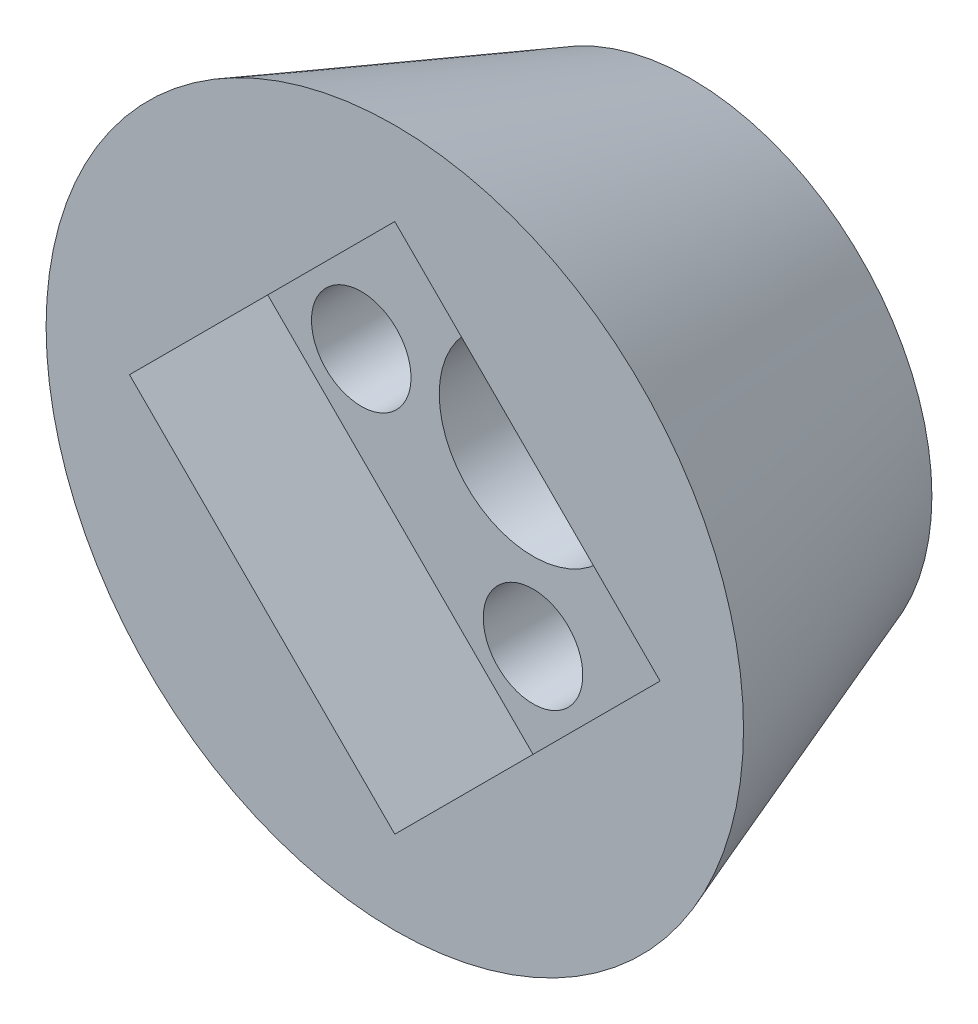
SolidWorks part; units mm, degrees
ref_plane "Front" through (0, 0, 0) normal (0, 0, 1) x (1, 0, 0)
ref_plane "Top" through (0, 0, 0) normal (0, 1, 0) x (1, 0, 0)
ref_plane "Right" through (0, 0, 0) normal (1, 0, 0) x (0, 0, -1)
sketch "GearFaceProfile" plane through (0, 0, 0) normal (0, 0, 1) x (1, 0, 0)
  circle A0 centre (0, 0) radius 12.2
  dimension "D1" = 24.4
extrude "GearFaceExtrude" add sketch "GearFaceProfile" along normal blind 15 draft 20 draft outward yes
sketch "CenterHoleProfile" plane through (0, 0, 0) normal (0, 0, -1) x (-1, 0, 0)
  circle A0 centre (0, 0) radius 4.75
  dimension "D1" = 9.5
extrude "CenterHoleCut" cut sketch "CenterHoleProfile" against normal through all
sketch "ScrewHoleProfile" plane through (0, 0, 0) normal (0, 0, -1) x (-1, 0, 0)
  line L0 (0, 0) -> (0, 8.7) construction
  line L1 (0, 0) -> (8.7, 0) construction
  line L2 (0, 0) -> (0, -8.7) construction
  line L3 (0, 0) -> (-8.7, 0) construction
  circle A2 centre (0, 8.7) radius 2.52
  circle A3 centre (8.7, 0) radius 2.52
  circle A4 centre (0, -8.7) radius 2.52
  circle A5 centre (-8.7, 0) radius 2.52
  dimension "D5" = 5.04
  dimension "D6" = 5.04
  dimension "D7" = 5.04
  dimension "D8" = 5.04
  dimension "D1" = 8.7
  dimension "D2" = 8.7
  dimension "D3" = 8.7
  dimension "D4" = 8.7
extrude "ScrewHoleCut" cut sketch "ScrewHoleProfile" against normal through all
sketch "ShaftCollarAttachmentProfile" plane through (0, 0, 15) normal (0, 0, 1) x (1, 0, 0)
  line L0 (0, 0) -> (0, 13.435) construction
  line L1 (0, 0) -> (13.435, 0) construction
  line L2 (0, 13.435) -> (13.435, 0)
  line L3 (13.435, 0) -> (0, -13.435)
  line L4 (0, -13.435) -> (-13.435, 0)
  line L5 (-13.435, 0) -> (0, 13.435)
  dimension "D1" = 19
  dimension "D2" = 19
extrude "ShaftCollarDockingCut" cut sketch "ShaftCollarAttachmentProfile" against normal blind 7
equation "\"TGMScrewHole-Center\"=8.70mm"
equation "\"TGMScrewHoleDiameter\"=5.04mm"
equation "\"TGMCenterHoleDiameter\"=9.50mm"
equation "\"TGMGearFaceDiameter\"=24.40mm"
equation "\"D1@GearFaceProfile\" = \"TGMGearFaceDiameter\""
equation "\"D1@CenterHoleProfile\" = \"TGMCenterHoleDiameter\""
equation "\"D4@ScrewHoleProfile\" = \"TGMScrewHole-Center\""
equation "\"D1@ScrewHoleProfile\" = \"TGMScrewHole-Center\""
equation "\"D2@ScrewHoleProfile\" = \"TGMScrewHole-Center\""
equation "\"D3@ScrewHoleProfile\" = \"TGMScrewHole-Center\""
equation "\"D5@ScrewHoleProfile\" = \"TGMScrewHoleDiameter\""
equation "\"D6@ScrewHoleProfile\" = \"TGMScrewHoleDiameter\""
equation "\"D8@ScrewHoleProfile\" = \"TGMScrewHoleDiameter\""
equation "\"D7@ScrewHoleProfile\" = \"TGMScrewHoleDiameter\""
equation "\"TGMCylinderLength\"=15.00mm"
equation "\"TGMShaftCollarSideLength\"=19.00mm"
equation "\"D1@ShaftCollarAttachmentProfile\" = \"TGMShaftCollarSideLength\""
equation "\"D2@ShaftCollarAttachmentProfile\" = \"TGMShaftCollarSideLength\""
equation "\"TGMShaftCollarDockingDepth\"=7.00mm"
equation "\"CageLeftBottomEdge\"=22.11mm"
equation "\"CageLeftTopEdge\"=22.11mm"
equation "\"CageRightBottomEdge\"=21.63mm"
equation "\"CageRightTopEdge\"=21.63mm"
equation "\"CageHeight\"=86.04mm"
equation "\"CageLength\"=73.76mm"
equation "\"CageTopScrewClearance\"=10mm"
equation "\"CageBottomScrewClearance\"=25mm"
equation "\"CageLeftTopDepth\"= 11.65mm"
equation "\"CageLeftBottomDepth\"=11.11mm"
equation "\"CageLeftTopHeight\"=8.56175mm"
equation "\"CageLeftBottomHeight\"=16mm"
equation "\"CageRightTopDepth\"= 11.05mm"
equation "\"CageRightBottomDepth\"=10.58mm"
equation "\"CageRightTopHeight\"=9.6mm"
equation "\"CageRightBottomHeight\"=15.49mm"
equation "\"CageLeftTopChannelDepth\"=2.41908mm"
equation "\"CageLeftBottomChannelDepth\"=2.588mm"
equation "\"CageLeftChannelHeight\"=11.7mm"
equation "\"CageRightTopChannelDepth\"=2.32mm"
equation "\"CageRightBottomChannelDepth\"=2.318mm"
equation "\"CageRightChannelHeight\"=10mm"
equation "\"CageChanRelHeight\"=23.99mm"
equation "\"CageChanRelDepth\"=5.492mm"
equation "\"CageChamberRadius\"=16.261mm"
equation "\"CageScrewDiameter\"=4.8mm"
equation "\"CageSetScrewDiameter\"=3.5mm"
equation "\"CageAxleRadius\"=6.639mm"
equation "\"CageAxleKeyHeight\"=1.619mm"
equation "\"CageAxleKeyWidth\"=2.662mm"
equation "\"CageHoseWindowWidth\"=16.29mm"
equation "\"CageHoseWindowHeight\"=26.5mm"
equation "\"CageHoseWindow-Edge\"=8.89mm"
equation "\"CageScrew-VerticalEdge\"=5.0mm"
equation "\"CageScrew-HorizontalEdge\"=7.5mm"
equation "\"CageScrew-HoseCornerScrewEdge\"=4.45mm"
equation "\"CageAxle-BottomEdge\"=56.05mm"
equation "\"CageAxle-FrontEdge\"=46.03mm"
equation "\"CageBackSetScrew-Axle\"=40mm"
equation "\"CageFrontSetScrew-Axle\"=22mm"
equation "\"CageVelocityWindow-BackEdge\"=34.8mm"
equation "\"CageVelocityWindow-BottomEdge\"=27.55mm"
equation "\"CageVelocityWindowHeight\"=22.29mm"
equation "\"CageVelocityWindowWidth\"=12.61mm"
equation "\"TriggerSlot-BottomEdge\"=6.35mm"
equation "\"TriggerSlot-FrontEdge\"=15mm"
equation "\"TriggerSlotSize\"=6.7mm"
equation "\"TriggerRackOffset\"=.236224in"
equation "\"TriggerSlotSizeInt\"=.25in"
equation "\"MotorMountLegLength\"=.25in"
equation "\"GearOffset\"=.264907in"
equation "\"TriggerSlotSpacing\"=.25in"
equation "\"TriggerMiniSlotWidth\"=3.5mm"
equation "\"TriggerRackWidth\"=6.5mm"
equation "\"whitemotordepth\"=11.27mm"
equation "\"whitemotorbackdepth\"=3.845mm"
equation "\"whitemotoraxledepth\" = 3.5mm"
equation "\"whitemotoraxleoffset\"=11.4mm"
equation "\"whitemotorwidth\"=12.07mm"
equation "\"whitemotorheight\"=16.68mm"
equation "\"whitemotorcylinderlength\" =13.04mm"
equation "\"whitemotorcylinderradius\"=3.845mm"
equation "\"whitemotorcylinderoffset\"=2.35mm"
equation "\"whitemotorcutoutlength\"=1.88mm"
equation "\"whitemotorouterrad\"=5mm"
equation "\"whitemotorinnerrad\"=2.95mm"
equation "\"elasticracklength\"=2in"
equation "\"elasticrackpegsize\"=.25in"
equation "\"elasticrackpegbuffer\"=.125in"
equation "\"elasticrackpegspacing\"=1.76476378in"
equation "\"elasticbaybuffer\"=.25in"
equation "\"elasticdepth\"=.125in"
equation "\"elasticbaydepth\"=.75in"
equation "\"motormountwidth\"=12mm"
equation "\"motormountcornerfillet\"=3mm"
equation "\"pandiscradius\"=14in"
equation "\"towermaterialwidth\"=.25in"
equation "\"towerslotlength\"=.5in"
equation "\"towermarkerspace\"=5in"
equation "\"towerslothorizoffset\"=1in"
equation "\"towerslothorizspacing\"=2in"
equation "\"towerslotvertoffset\"=3in"
equation "\"towerslotvertspacing\"=1in"
equation "\"towerheight\"=12in"
equation "\"towerupslot\"=1in"
equation "\"toweraxle\"=.5in"
equation "\"towerplatslotoffset\"=1.5in"
equation "\"towermotorpanelheight\"=10in"
equation "\"towerplatdepth\"=2in"
equation "\"stepperouterrad\"=10mm"
equation "\"stepperscrewsize\"=3.45mm"
equation "\"stepperscrewc2c\"=49.5mm"
equation "\"stepperdepthoffset\"=24mm"
equation "\"stepperhorizoffset\"=22.91mm"
equation "\"shaftslotOD\"=18.8mm"
equation "\"shaftslotID\"=13.28mm"
equation "\"shaftkeywidth\"=2.67mm"
equation "\"shaftkeydepth\"=1.8mm"
equation "\"shaftcollartotaldepth\"=12.5mm"
equation "\"shaftsquaredepth\"=6mm"
equation "\"shaftsetscrewsize\"=3.5mm"
equation "\"shaftkeytightdepth\"=1.85mm"
equation "\"shaftslottightID\"=12.78mm"
equation "\"shaftsetscrewoffset\"=9mm"
equation "\"cagecollartotaldepth\"=10mm"
equation "\"cagecollartotalwidth\"=35mm"
equation "\"cagecollarbasedepth\"=4mm"
equation "\"ajaxaxlesize\"=3.87mm"
equation "\"ajaxinnercut\"=2.3mm"
equation "\"ajaxwidth\"=6.1mm"
equation "\"ajaxdiametral\"=25.8854"
equation "\"ajax4020gap\"=29.5mm"
equation "\"ajax4010gap\"=24.5mm"
equation "\"ajaxhubdepth\"=.25in"
equation "\"ajaxcutoutdepth\"=2.3mm"
equation "\"ajax20hubbuffer\"=0.240157in"
equation "\"ajax20hubholeoffset\"=.19685in"
equation "\"ajax20hubholesize\"=.059055in"
equation "\"ajax20cutoutint\"=13.4mm"
equation "\"ajax40hubholesize\"=7.21mm"
equation "\"ajax40hubholeoffset\"=10mm"
equation "\"ajax40hubbuffer\"=.350394in"
equation "\"ajax40cutoutint\"=32.6mm"
equation "\"no6diam\"=.146in"
equation "\"shconangle\"=20deg"
equation "\"shconlen\"=1in"
equation "\"lnconlen\"=1.5in"
equation "\"lnconangle\"=15deg"
